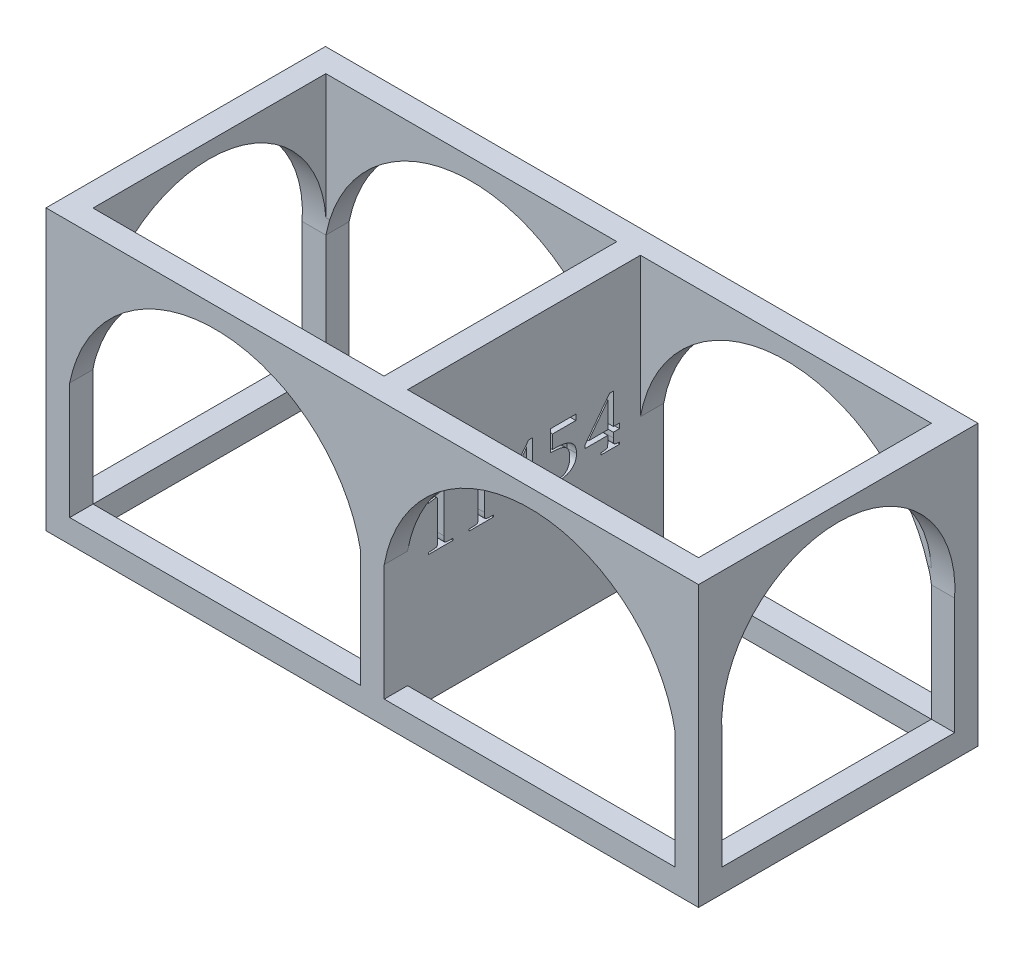
SolidWorks part; units mm, degrees
ref_plane "Front Plane" through (0, 0, 0) normal (0, 0, 1) x (1, 0, 0)
ref_plane "Top Plane" through (0, 0, 0) normal (0, 1, 0) x (1, 0, 0)
ref_plane "Right Plane" through (0, 0, 0) normal (1, 0, 0) x (0, 0, -1)
sketch "Sketch1" plane through (0, 0, 0) normal (0, 1, 0) x (1, 0, 0)
  line L1 (0, 0) -> (177.8, 0)
  line L2 (0, 0) -> (0, -6.35)
  line L3 (0, -6.35) -> (177.8, -6.35)
  line L4 (177.8, 0) -> (177.8, -6.35)
  dimension "D1" = 177.8
  dimension "D2" = 6.35
extrude "Boss-Extrude1" add sketch "Sketch1" along normal blind 6.35 contours L3 L4 L1 L2
sketch "Sketch2" plane through (0, 0, 0) normal (0, -1, 0) x (-1, 0, 0)
  line L1 (-177.8, 0) -> (-171.45, 0)
  line L2 (-177.8, 0) -> (-177.8, -76.1492)
  line L3 (-177.8, -76.1492) -> (-171.45, -76.1492)
  line L4 (-171.45, 0) -> (-171.45, -76.1492)
  dimension "D1" = 6.35
extrude "Boss-Extrude3" add sketch "Sketch2" against normal blind 6.35
sketch "Sketch3" plane through (0, 0, 0) normal (0, -1, 0) x (1, 0, 0)
  line L1 (177.8, 76.1492) -> (0, 76.1492)
  line L2 (177.8, 76.1492) -> (177.8, 69.7992)
  line L3 (177.8, 69.7992) -> (0, 69.7992)
  line L4 (0, 76.1492) -> (0, 69.7992)
  dimension "D1" = 6.35
extrude "Boss-Extrude4" add sketch "Sketch3" against normal blind 6.35
sketch "Sketch4" plane through (0, 0, 0) normal (0, -1, 0) x (-1, 0, 0)
  line L0 (-177.8, -76.1492) -> (0, -76.1492) construction
  line L1 (0, 0) -> (-6.4539, 0)
  line L2 (0, 0) -> (0, -76.1492)
  line L3 (0, -76.1492) -> (-6.4539, -76.1492)
  line L4 (-6.4539, 0) -> (-6.4539, -76.1492)
extrude "Boss-Extrude5" add sketch "Sketch4" against normal blind 6.35
sketch "Sketch5" plane through (0, 0, 0) normal (0, -1, 0) x (-1, 0, 0)
  line L3 (0, 0) -> (-177.8, 0) construction
  line L4 (-92.1627, -76.1492) -> (-85.7412, -76.1492)
  line L5 (-92.1627, -76.1492) -> (-92.1627, 0)
  line L6 (-92.1627, 0) -> (-85.7412, 0)
  line L7 (-85.7412, -76.1492) -> (-85.7412, 0)
  line L8 (-92.1627, -76.1492) -> (-85.7412, 0) construction
  line L9 (-92.1627, 0) -> (-85.7412, -76.1492) construction
  point P6 (-88.9519, -38.0746)
extrude "Boss-Extrude6" add sketch "Sketch5" against normal blind 76.2
sketch "Sketch6" plane through (0, 0, 0) normal (0, -1, 0) x (-1, 0, 0)
  line L1 (0, -76.1492) -> (-6.4539, -76.1492)
  line L2 (0, -76.1492) -> (0, -69.7992)
  line L3 (0, -69.7992) -> (-6.4539, -69.7992)
  line L4 (-6.4539, -76.1492) -> (-6.4539, -69.7992)
extrude "Boss-Extrude7" add sketch "Sketch6" against normal blind 76.2
sketch "Sketch7" plane through (0, 0, 0) normal (0, -1, 0) x (-1, 0, 0)
  line L1 (0, 0) -> (-6.4539, 0)
  line L2 (0, 0) -> (0, -6.35)
  line L3 (0, -6.35) -> (-6.4539, -6.35)
  line L4 (-6.4539, 0) -> (-6.4539, -6.35)
extrude "Boss-Extrude8" add sketch "Sketch7" against normal blind 76.2
sketch "Sketch8" plane through (0, 0, 0) normal (0, -1, 0) x (-1, 0, 0)
  line L1 (-177.8, 0) -> (-171.45, 0)
  line L2 (-177.8, 0) -> (-177.8, -6.35)
  line L3 (-177.8, -6.35) -> (-171.45, -6.35)
  line L4 (-171.45, 0) -> (-171.45, -6.35)
extrude "Boss-Extrude9" add sketch "Sketch8" against normal blind 76.2
sketch "Sketch9" plane through (0, 0, 0) normal (0, -1, 0) x (-1, 0, 0)
  line L1 (-177.8, -76.1492) -> (-171.45, -76.1492)
  line L2 (-177.8, -76.1492) -> (-177.8, -69.7992)
  line L3 (-177.8, -69.7992) -> (-171.45, -69.7992)
  line L4 (-171.45, -76.1492) -> (-171.45, -69.7992)
extrude "Boss-Extrude10" add sketch "Sketch9" against normal blind 76.2
sketch "Sketch10" plane through (0, 76.2, 0) normal (0, 1, 0) x (1, 0, 0)
  line L1 (0, -76.1492) -> (6.4539, -76.1492)
  line L2 (0, -76.1492) -> (0, 0)
  line L3 (0, 0) -> (6.4539, 0)
  line L4 (6.4539, -76.1492) -> (6.4539, 0)
extrude "Boss-Extrude11" add sketch "Sketch10" against normal blind 6.35
sketch "Sketch11" plane through (0, 76.2, 0) normal (0, 1, 0) x (1, 0, 0)
  line L1 (171.45, -76.1492) -> (177.8, -76.1492)
  line L2 (171.45, -76.1492) -> (171.45, 0)
  line L3 (171.45, 0) -> (177.8, 0)
  line L4 (177.8, -76.1492) -> (177.8, 0)
extrude "Boss-Extrude12" add sketch "Sketch11" against normal blind 6.35
sketch "Sketch12" plane through (0, 69.85, 0) normal (0, -1, 0) x (-1, 0, 0)
  line L1 (-6.4539, -6.35) -> (-171.7776, -6.35)
  line L2 (-6.4539, -6.35) -> (-6.4539, 0)
  line L3 (-6.4539, 0) -> (-171.7776, 0)
  line L4 (-171.7776, -6.35) -> (-171.7776, 0)
extrude "Boss-Extrude13" add sketch "Sketch12" against normal blind 6.35
sketch "Sketch13" plane through (0, 0, 0) normal (-1, 0, 0) x (0, 0, 1)
  line L1 (69.7992, 69.85) -> (76.1492, 69.85)
  line L2 (69.7992, 69.85) -> (69.7992, 76.2)
  line L3 (69.7992, 76.2) -> (76.1492, 76.2)
  line L4 (76.1492, 69.85) -> (76.1492, 76.2)
extrude "Boss-Extrude14" add sketch "Sketch13" against normal blind 175.26
sketch "Sketch16" plane through (92.1627, 0, 0) normal (1, 0, 0) x (0, 0, -1)
  text T0 "11454\r\n" font "Lucida Bright" height in points 48
extrude "Cut-Extrude1" cut sketch "Sketch16" against normal blind 2.54
sketch "Sketch22" plane through (6.4539, 0, 0) normal (1, 0, 0) x (0, 0, -1)
  line L0 (0, 69.85) -> (0, 6.35) construction
  line L1 (0, 38.1) -> (-6.35, 38.1)
  line L2 (0, 38.1) -> (0, 69.85)
  line L3 (0, 69.85) -> (-6.35, 69.85)
  line L4 (-6.35, 38.1) -> (-6.35, 69.85)
extrude "Boss-Extrude16" add sketch "Sketch22" along normal blind 165.1
sketch "Sketch23" plane through (0, 0, 0) normal (0, 0, -1) x (-1, 0, 0)
  line L0 (-171.45, 38.1) -> (-92.1627, 38.1)
  arc A0 (-171.45, 38.1) -> (-92.1627, 38.1) centre (-131.8063, 30.9203) cw
extrude "Cut-Extrude3" cut sketch "Sketch23" against normal blind 165.1
sketch "Sketch24" plane through (0, 0, 0) normal (0, 0, -1) x (-1, 0, 0)
  line L0 (-85.7412, 38.1) -> (-6.4539, 38.1)
  arc A0 (-85.7412, 38.1) -> (-6.4539, 38.1) centre (-46.0976, 30.2103) cw
extrude "Cut-Extrude4" cut sketch "Sketch24" against normal blind 165.1
sketch "Sketch26" plane through (171.45, 0, 0) normal (-1, 0, 0) x (0, 0, 1)
  line L0 (76.1492, 69.85) -> (76.1492, 6.35) construction
  line L1 (69.7992, 69.85) -> (76.1492, 69.85)
  line L2 (69.7992, 69.85) -> (69.7992, 38.1)
  line L3 (69.7992, 38.1) -> (76.1492, 38.1)
  line L4 (76.1492, 69.85) -> (76.1492, 38.1)
extrude "Boss-Extrude17" add sketch "Sketch26" along normal blind 165.1
sketch "Sketch27" plane through (0, 0, 76.1492) normal (0, 0, 1) x (1, 0, 0)
  line L0 (6.4539, 38.1) -> (85.7412, 38.1)
  arc A0 (6.4539, 38.1) -> (85.7412, 38.1) centre (46.0976, 30.2103) cw
extrude "Cut-Extrude5" cut sketch "Sketch27" against normal blind 165.1
sketch "Sketch28" plane through (0, 0, 76.1492) normal (0, 0, 1) x (1, 0, 0)
  line L0 (92.1627, 38.1) -> (171.45, 38.1)
  arc A0 (92.1627, 38.1) -> (171.45, 38.1) centre (131.8063, 30.9203) cw
extrude "Cut-Extrude6" cut sketch "Sketch28" against normal blind 165.1
sketch "Sketch29" plane through (0, 0, 6.35) normal (0, 0, 1) x (1, 0, 0)
  line L1 (6.4539, 38.1) -> (0, 38.1)
  line L2 (6.4539, 38.1) -> (6.4539, 69.85)
  line L3 (6.4539, 69.85) -> (0, 69.85)
  line L4 (0, 38.1) -> (0, 69.85)
extrude "Boss-Extrude18" add sketch "Sketch29" along normal blind 65.278
sketch "Sketch30" plane through (0, 0, 0) normal (-1, 0, 0) x (0, 0, 1)
  line L0 (6.35, 38.1) -> (69.7992, 38.1)
  arc A0 (6.35, 38.1) -> (69.7992, 38.1) centre (38.0746, 40.1702) cw
extrude "Cut-Extrude7" cut sketch "Sketch30" against normal blind 65.278
sketch "Sketch31" plane through (0, 0, 69.7992) normal (0, 0, -1) x (-1, 0, 0)
  line L1 (-177.8, 69.85) -> (-171.45, 69.85)
  line L2 (-177.8, 69.85) -> (-177.8, 38.1)
  line L3 (-177.8, 38.1) -> (-171.45, 38.1)
  line L4 (-171.45, 69.85) -> (-171.45, 38.1)
extrude "Boss-Extrude19" add sketch "Sketch31" along normal blind 65.278
sketch "Sketch32" plane through (177.8, 0, 0) normal (1, 0, 0) x (0, 0, -1)
  line L0 (-69.7992, 38.1) -> (-6.35, 38.1)
  arc A0 (-69.7992, 38.1) -> (-6.35, 38.1) centre (-38.0746, 40.1059) cw
extrude "Cut-Extrude8" cut sketch "Sketch32" against normal blind 65.278
